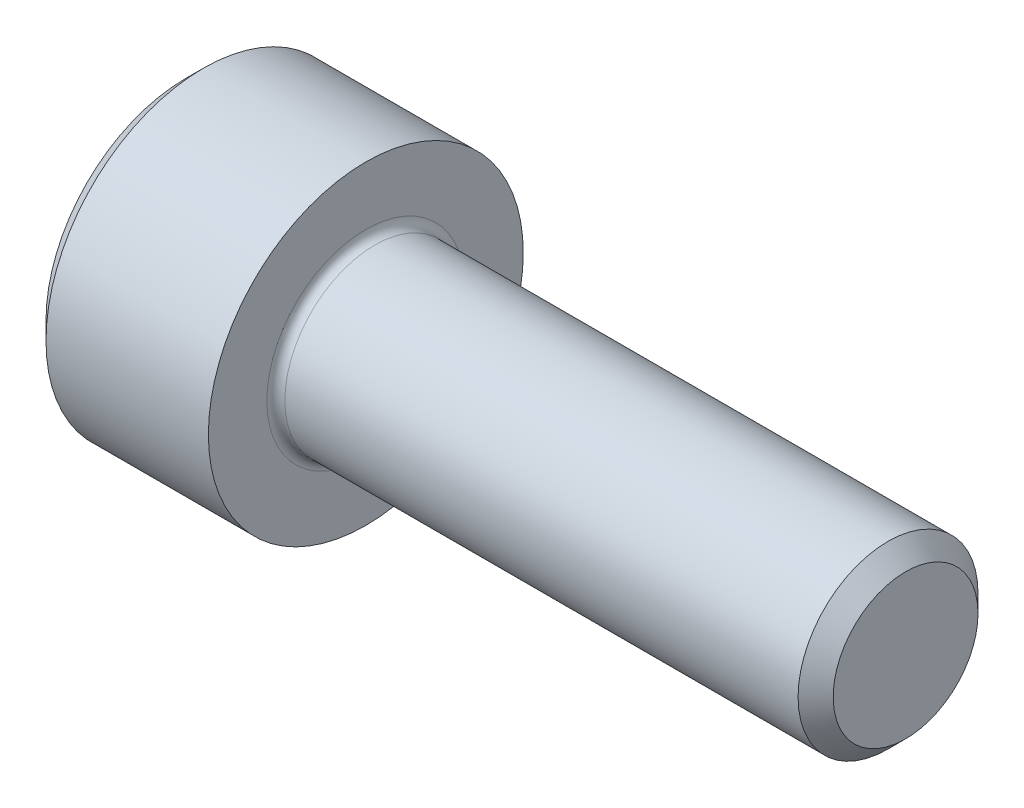
SolidWorks part; units mm, degrees
material "Plain Carbon Steel"
ref_plane "Front Plane" through (0, 0, 0) normal (0, 0, 1) x (1, 0, 0)
ref_plane "Top Plane" through (0, 0, 0) normal (0, 1, 0) x (1, 0, 0)
ref_plane "Right Plane" through (0, 0, 0) normal (1, 0, 0) x (0, 0, -1)
ref_plane "Plane1" through (0, 0, 0) normal (0, 0, -1) x (-1, 0, 0)
sketch "Sketch1" plane through (0, 0, 0) normal (0, 0, -1) x (-1, 0, 0)
  line L0 (-4, 3.5) -> (-4, 0)
  line L1 (-4, 0) -> (0, 0)
  line L2 (0, 0) -> (0, 3.5)
  line L3 (0, 3.5) -> (-4, 3.5)
  line L4 (-4, 0) -> (0, 0) construction
revolve "Revolve1" add sketch "Sketch1" angle 360 about L4
sketch "Sketch2" plane through (4, 0, 0) normal (1, 0, 0) x (0, 0, -1)
  circle A0 centre (0, 0) radius 2
extrude "Boss-Extrude1" add sketch "Sketch2" along normal blind 12
sketch "Sketch3" plane through (0, 0, 0) normal (-1, 0, 0) x (0, 0, 1)
  line L0 (1.5355, -0.8865) -> (1.5355, 0.8865)
  line L1 (1.5355, 0.8865) -> (0, 1.773)
  line L2 (0, 1.773) -> (-1.5355, 0.8865)
  line L3 (-1.5355, 0.8865) -> (-1.5355, -0.8865)
  line L4 (-1.5355, -0.8865) -> (0, -1.773)
  line L5 (0, -1.773) -> (1.5355, -0.8865)
extrude "Cut-Extrude1" cut sketch "Sketch3" against normal blind 2
sketch "Sketch4" plane through (0, 0, 0) normal (0, 0, 1) x (1, 0, 0)
  line L0 (2, 1.5355) -> (2, 0)
  line L1 (2, 0) -> (2.8865, 0)
  line L2 (2.8865, 0) -> (2, 1.5355)
  line L3 (2, 0) -> (2.8865, 0) construction
revolve "Cut-Revolve1" cut sketch "Sketch4" angle 360 about L3
chamfer "Chamfer1" distance 0.39 angle 45 2 edges at (0, 0, 3.5) (16, 0, -2)
fillet "Fillet1" radius 0.2 1 edges at (4, 0, -2)
